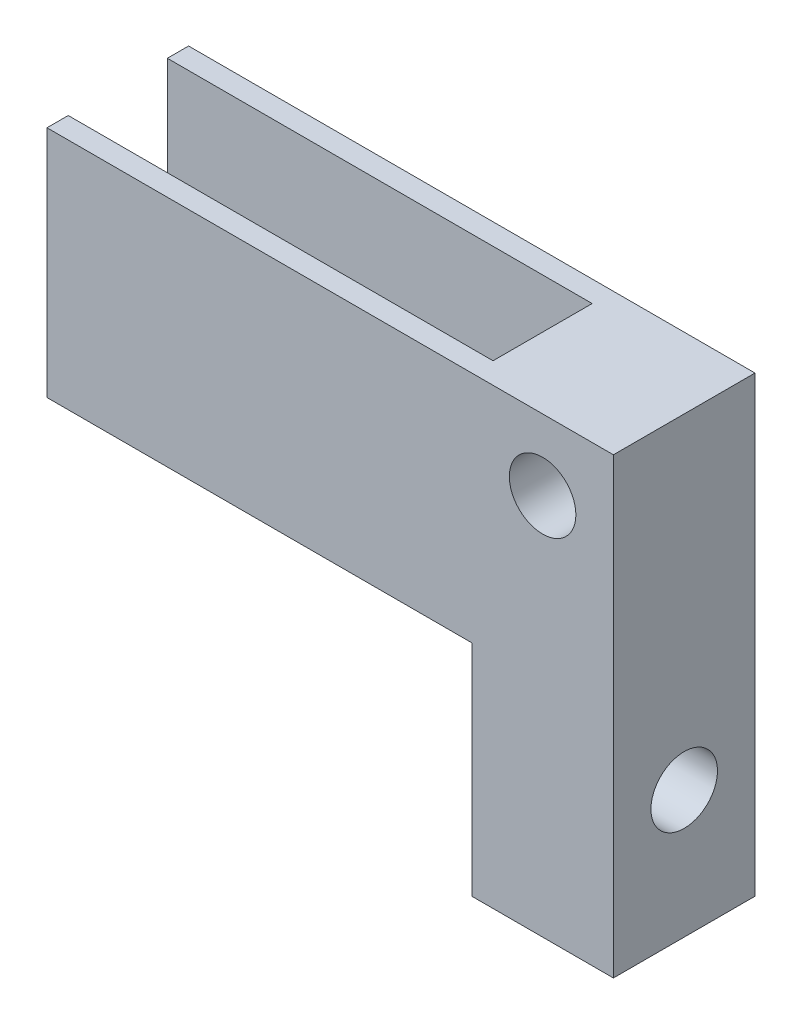
SolidWorks part; units mm, degrees
ref_plane "Front Plane" through (0, 0, 0) normal (0, 0, 1) x (1, 0, 0)
ref_plane "Top Plane" through (0, 0, 0) normal (0, 1, 0) x (1, 0, 0)
ref_plane "Right Plane" through (0, 0, 0) normal (1, 0, 0) x (0, 0, -1)
sketch "Sketch2" plane through (0, 0, 0) normal (0, 0, 1) x (1, 0, 0)
  line L8 (0, 0) -> (0, 50)
  line L9 (0, 50) -> (10, 50)
  line L10 (10, 50) -> (10, 0)
  line L11 (10, 0) -> (0, 0)
  dimension "D1" = 50
  dimension "D2" = 10
extrude "Boss-Extrude1" add sketch "Sketch2" along normal blind 10 contours L11 L8 L9 L10
sketch "Sketch6" plane through (0, 0, 10) normal (0, 0, 1) x (1, 0, 0)
  line L0 (10, 50) -> (10, 0) construction
  line L1 (10, 0) -> (0, 0) construction
  circle A0 centre (5, 27) radius 2.35
  dimension "D1" = 4.7
  dimension "D2" = 5
  dimension "D3" = 27
extrude "Cut-Extrude3" cut sketch "Sketch6" against normal through all contours A0
sketch "Sketch7" plane through (0, 0, 0) normal (-1, 0, 0) x (0, 0, 1)
  line L0 (10, 0) -> (10, 50) construction
  line L1 (10, 0) -> (0, 0) construction
  circle A0 centre (5, 41) radius 2.35
  circle A1 centre (5, 9) radius 2.35
  dimension "D3" = 4.7
  dimension "D4" = 4.7
  dimension "D5" = 9
  dimension "D1" = 32
  dimension "D2" = 5
  dimension "D6" = 5
extrude "Cut-Extrude4" cut sketch "Sketch7" against normal through all
sketch "Sketch8" plane through (0, 0, 0) normal (-1, 0, 0) x (0, 0, 1)
  line L0 (8.5, 36.5) -> (8.5, 15.5)
  line L1 (8.5, 15.5) -> (10, 15.5)
  line L2 (10, 0) -> (10, 50) construction
  line L3 (10, 15.5) -> (10, 36.5)
  line L4 (10, 36.5) -> (8.5, 36.5)
  line L5 (1.5, 36.5) -> (1.5, 15.5)
  line L6 (1.5, 15.5) -> (0, 15.5)
  line L7 (0, 0) -> (0, 50) construction
  line L8 (0, 15.5) -> (0, 36.5)
  line L9 (0, 36.5) -> (1.5, 36.5)
  line L10 (10, 50) -> (0, 50) construction
  dimension "D1" = 1.5
  dimension "D2" = 1.5
  dimension "D3" = 13.5
  dimension "D4" = 21
extrude "Boss-Extrude2" add sketch "Sketch8" along normal blind 30
sketch "Sketch9" plane through (0, 0, 10) normal (0, 0, 1) x (1, 0, 0)
  line L0 (10, 0) -> (0, 0) construction
  line L1 (-34.1392, 32) -> (18.855, 32)
  line L2 (-34.1392, 32) -> (-34.1392, 51.0598)
  line L3 (-34.1392, 51.0598) -> (18.855, 51.0598)
  line L4 (18.855, 32) -> (18.855, 51.0598)
  dimension "D1" = 32
extrude "Cut-Extrude5" cut sketch "Sketch9" against normal through all
